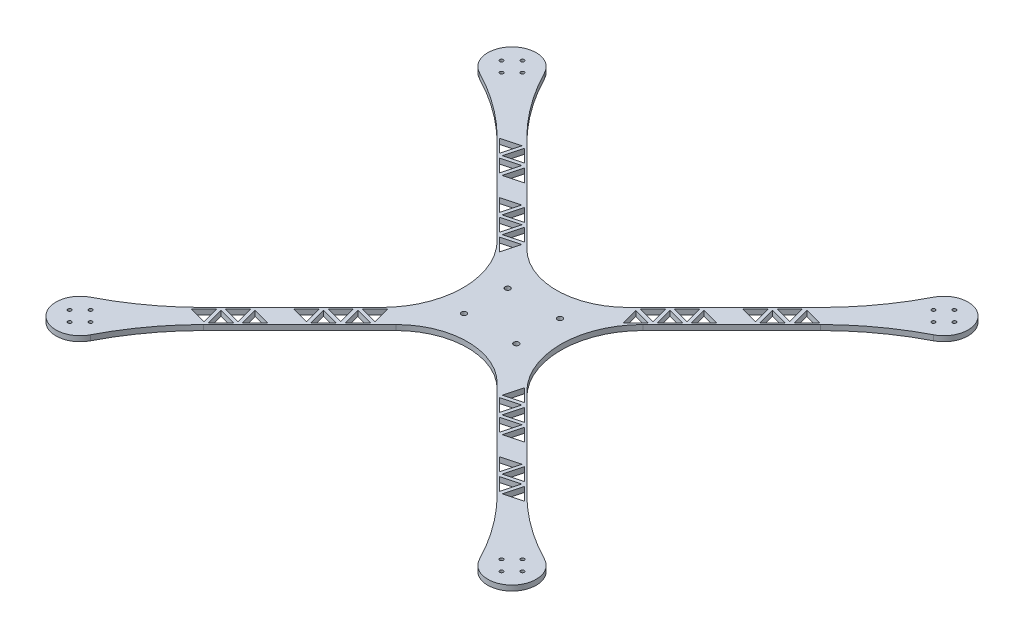
SolidWorks part; units mm, degrees
ref_plane "Front Plane" through (0, 0, 0) normal (0, 0, 1) x (1, 0, 0)
ref_plane "Top Plane" through (0, 0, 0) normal (0, 1, 0) x (1, 0, 0)
ref_plane "Right Plane" through (0, 0, 0) normal (1, 0, 0) x (0, 0, -1)
sketch "Sketch1" plane through (0, 0, 0) normal (0, 1, 0) x (1, 0, 0)
  line L0 (-18, 0) -> (18, 0) construction
  line L1 (-15, -15.5) -> (15, -15.5)
  line L2 (-18, -12.5) -> (-18, 12.5)
  line L3 (-15, 15.5) -> (15, 15.5)
  line L4 (18, -12.5) -> (18, 12.5)
  line L5 (-28, -12.5) -> (-28, 12.5)
  line L6 (-15, 25.5) -> (15, 25.5)
  line L7 (0, -15.5) -> (0, 15.5) construction
  line L8 (28, -12.5) -> (28, 12.5)
  line L9 (-15, -25.5) -> (15, -25.5)
  line L10 (123.7437, -123.7437) -> (-123.7437, 123.7437) construction
  line L11 (123.7437, 123.7437) -> (-123.7437, -123.7437) construction
  line L12 (127.9863, -119.501) -> (-119.501, 127.9863)
  line L13 (119.501, 127.9863) -> (-127.9863, -119.501)
  line L14 (119.501, -127.9863) -> (-127.9863, 119.501)
  line L15 (127.9863, 119.501) -> (-119.501, -127.9863)
  line L16 (-262.828, 0) -> (262.828, 0) construction
  circle A0 centre (15, 12.5) radius 1.5
  circle A1 centre (15, -12.5) radius 1.5
  circle A2 centre (-15, -12.5) radius 1.5
  circle A3 centre (-15, 12.5) radius 1.5
  arc A4 (15, 15.5) -> (18, 12.5) centre (15, 12.5) cw
  arc A5 (15, -15.5) -> (18, -12.5) centre (15, -12.5) ccw
  arc A6 (-15, -15.5) -> (-18, -12.5) centre (-15, -12.5) cw
  arc A7 (-18, 12.5) -> (-15, 15.5) centre (-15, 12.5) cw
  arc A12 (-28, 12.5) -> (-15, 25.5) centre (-15, 12.5) cw construction
  arc A13 (-15, -25.5) -> (-28, -12.5) centre (-15, -12.5) cw construction
  arc A14 (15, -25.5) -> (28, -12.5) centre (15, -12.5) ccw construction
  arc A15 (15, 25.5) -> (28, 12.5) centre (15, 12.5) cw construction
  circle A16 centre (123.7437, 123.7437) radius 13.85
  circle A17 centre (123.7437, -123.7437) radius 13.85
  circle A18 centre (-123.7437, -123.7437) radius 13.85
  circle A19 centre (-123.7437, 123.7437) radius 13.85
  arc A20 (111.4203, 130.0648) -> (84.1457, 92.631) centre (-21.4329, 198.2096) cw
  arc A21 (130.0648, 111.4203) -> (92.631, 84.1457) centre (198.2096, -21.4329) ccw
  arc A22 (41.799, 33.3137) -> (41.799, -33.3137) centre (75.1127, 0) ccw
  arc A23 (-41.799, 33.3137) -> (-41.799, -33.3137) centre (-75.1127, 0) cw
  arc A24 (111.4203, -130.0648) -> (84.1457, -92.631) centre (-21.4329, -198.2096) ccw
  arc A25 (130.0648, -111.4203) -> (92.631, -84.1457) centre (198.2096, 21.4329) cw
  arc A26 (-111.4203, 130.0648) -> (-84.1457, 92.631) centre (21.4329, 198.2096) ccw
  arc A27 (-130.0648, 111.4203) -> (-92.631, 84.1457) centre (-198.2096, -21.4329) cw
  arc A28 (-111.4203, -130.0648) -> (-84.1457, -92.631) centre (21.4329, -198.2096) cw
  arc A29 (-130.0648, -111.4203) -> (-92.631, -84.1457) centre (-198.2096, 21.4329) ccw
  arc A30 (-29.0459, 37.5312) -> (29.0459, 37.5312) centre (0, 66.5772) ccw
  arc A31 (-29.0459, -37.5312) -> (29.0459, -37.5312) centre (0, -66.5772) cw
  circle A32 centre (123.7437, 123.7437) radius 6 construction
  circle A36 centre (123.7437, 129.7437) radius 1
  circle A37 centre (129.7437, 123.7437) radius 1
  circle A38 centre (123.7437, 117.7437) radius 1
  circle A39 centre (117.7437, 123.7437) radius 1
  circle A40 centre (123.7437, -123.7437) radius 6 construction
  circle A41 centre (123.7437, -117.7437) radius 1
  circle A42 centre (129.7437, -123.7437) radius 1
  circle A43 centre (123.7437, -129.7437) radius 1
  circle A44 centre (117.7437, -123.7437) radius 1
  circle A45 centre (-123.7437, -123.7437) radius 6 construction
  circle A46 centre (-123.7437, -117.7437) radius 1
  circle A47 centre (-117.7437, -123.7437) radius 1
  circle A48 centre (-123.7437, -129.7437) radius 1
  circle A49 centre (-129.7437, -123.7437) radius 1
  circle A50 centre (-123.7437, 123.7437) radius 6 construction
  circle A51 centre (-123.7437, 129.7437) radius 1
  circle A52 centre (-117.7437, 123.7437) radius 1
  circle A53 centre (-123.7437, 117.7437) radius 1
  circle A54 centre (-129.7437, 123.7437) radius 1
  point P0 (0, 0)
  point P41 (0, 0)
  point P44 (0, 0)
  point P93 (-109.7065, 109.7065)
  point P99 (0, 0)
  point P108 (123.7437, 123.7437)
  point P118 (123.7437, -123.7437)
  point P128 (-123.7437, -123.7437)
  point P138 (-123.7437, 123.7437)
  dimension "D3" = 3
  dimension "D6" = 3
  dimension "D14" = 27.7
  dimension "D16" = 2
  dimension "D18" = 4
  dimension "D19" = 4
  dimension "D20" = 4
  dimension "D1" = 31
  dimension "D2" = 36
  dimension "D4" = 3
  dimension "D5" = 3
  dimension "D7" = 10
  dimension "D8" = 350
  dimension "D9" = 350
  dimension "D10" = 45
  dimension "D11" = 45
  dimension "D15" = 50
  dimension "D17" = 4
  dimension "D12" = 6
  dimension "D13" = 6
extrude "Boss-Extrude1" add sketch "Sketch1" along normal blind 3
sketch "Sketch3" plane through (0, 3, 0) normal (0, 1, 0) x (1, 0, 0)
  line L0 (-70.4196, 78.9048) -> (-83.8038, 75.3185)
  line L1 (-83.8038, 75.3185) -> (-74.0059, 65.5206)
  line L2 (-41.799, 33.3137) -> (-92.631, 84.1457) construction
  line L3 (-80.2201, 88.7053) -> (-93.6043, 85.119)
  line L8 (-93.6043, 85.119) -> (-83.8064, 75.3211)
  line L9 (-83.8064, 75.3211) -> (-80.2201, 88.7053)
  line L10 (-29.0459, 37.5312) -> (-84.1457, 92.631) construction
  line L11 (-123.7437, 123.7437) -> (0, 0) construction
  line L12 (-81.6343, 87.2911) -> (-91.6725, 84.6014)
  line L13 (-91.6725, 84.6014) -> (-84.324, 77.2529)
  line L14 (-84.324, 77.2529) -> (-81.6343, 87.2911)
  line L15 (-74.0059, 65.5206) -> (-70.4196, 78.9048)
  line L16 (-71.8338, 77.4906) -> (-81.872, 74.8009)
  line L17 (-81.872, 74.8009) -> (-74.5235, 67.4524)
  line L18 (-74.5235, 67.4524) -> (-71.8338, 77.4906)
  line L19 (-60.6191, 69.1043) -> (-74.0033, 65.518)
  line L20 (-74.0033, 65.518) -> (-64.2054, 55.7201)
  line L21 (-64.2054, 55.7201) -> (-60.6191, 69.1043)
  line L22 (-62.0333, 67.6901) -> (-72.0715, 65.0004)
  line L23 (-72.0715, 65.0004) -> (-64.723, 57.6519)
  line L24 (-64.723, 57.6519) -> (-62.0333, 67.6901)
  line L25 (-50.8186, 59.3038) -> (-64.2028, 55.7175)
  line L26 (-64.2028, 55.7175) -> (-54.4049, 45.9196)
  line L27 (-54.4049, 45.9196) -> (-50.8186, 59.3038)
  line L28 (-52.2328, 57.8896) -> (-62.271, 55.1999)
  line L29 (-62.271, 55.1999) -> (-54.9225, 47.8514)
  line L30 (-54.9225, 47.8514) -> (-52.2328, 57.8896)
  line L31 (-41.0181, 49.5033) -> (-54.4023, 45.917)
  line L32 (-54.4023, 45.917) -> (-44.6044, 36.1191)
  line L33 (-44.6044, 36.1191) -> (-41.0181, 49.5033)
  line L34 (-42.4323, 48.0891) -> (-52.4705, 45.3994)
  line L35 (-52.4705, 45.3994) -> (-45.122, 38.0509)
  line L36 (-45.122, 38.0509) -> (-42.4323, 48.0891)
  line L37 (-31.2176, 39.7028) -> (-44.6018, 36.1165)
  line L38 (-44.6018, 36.1165) -> (-34.8039, 26.3186)
  line L39 (-34.8039, 26.3186) -> (-31.2176, 39.7028)
  line L40 (-32.6318, 38.2886) -> (-42.67, 35.5989)
  line L41 (-42.67, 35.5989) -> (-35.3215, 28.2504)
  line L42 (-35.3215, 28.2504) -> (-32.6318, 38.2886)
  line L43 (-80.2201, 88.7053) -> (-31.2176, 39.7028)
  line L44 (-59.2048, 70.5186) -> (-74.2621, 66.484) construction
  line L45 (-79.7024, 86.7735) -> (-72.3514, 79.4225)
  line L46 (-33.1494, 40.2205) -> (-43.1911, 37.5298)
  line L47 (-73.0399, 65.2618) -> (-72.8914, 65.816)
  line L48 (-72.3514, 79.4225) -> (-82.3931, 76.7318)
  line L49 (-63.2394, 55.4613) -> (-63.0909, 56.0155)
  line L50 (-62.5509, 69.622) -> (-72.5926, 66.9313)
  line L51 (-52.9916, 47.3303) -> (-50.3009, 57.372)
  line L52 (-52.7504, 59.8215) -> (-62.7921, 57.1308)
  line L53 (-43.1911, 37.5298) -> (-40.5004, 47.5715)
  line L54 (-42.9499, 50.021) -> (-52.9916, 47.3303)
  line L55 (-73.0399, 65.2618) -> (-69.0053, 80.3191) construction
  line L56 (-69.0053, 80.3191) -> (-84.0626, 76.2845) construction
  line L57 (-69.9019, 76.973) -> (-62.5509, 69.622)
  line L58 (-79.7024, 86.7735) -> (-33.1494, 40.2205) construction
  line L59 (-82.3931, 76.7318) -> (-79.7024, 86.7735)
  line L60 (-82.8404, 75.0623) -> (-79.7024, 86.7735) construction
  line L61 (-63.2394, 55.4613) -> (-59.2048, 70.5186) construction
  line L62 (-49.4043, 60.7181) -> (-64.4616, 56.6835) construction
  line L63 (-53.4389, 45.6608) -> (-49.4043, 60.7181) construction
  line L64 (-39.6038, 50.9176) -> (-54.6611, 46.883) construction
  line L65 (-43.6384, 35.8603) -> (-39.6038, 50.9176) construction
  line L66 (-60.1014, 67.1725) -> (-52.7504, 59.8215)
  line L67 (-50.3009, 57.372) -> (-42.9499, 50.021)
  line L68 (-40.5004, 47.5715) -> (-33.1494, 40.2205)
  line L69 (-62.7921, 57.1308) -> (-60.1014, 67.1725)
  line L70 (-33.1494, 40.2205) -> (-44.8606, 37.0825) construction
  line L71 (-63.9074, 56.832) -> (-64.4616, 56.6835)
  line L72 (-72.5926, 66.9313) -> (-69.9019, 76.973)
  line L73 (-73.7079, 66.6325) -> (-74.2621, 66.484)
  line L74 (-58.2257, -49.7404) -> (-68.0236, -59.5383)
  line L75 (-68.0262, -59.5409) -> (-77.8241, -69.3388)
  line L76 (-97.4251, -88.9398) -> (-84.0408, -92.5261)
  line L77 (-57.1112, -50.0358) -> (-57.2597, -49.4816)
  line L78 (-35.0383, -43.5236) -> (-38.6247, -30.1394)
  line L79 (-95.4933, -88.4222) -> (-85.4551, -91.1119)
  line L80 (-63.9222, -70.9933) -> (-66.6129, -60.9516)
  line L81 (-66.0918, -59.0207) -> (-56.0536, -61.7104)
  line L82 (-75.6546, -81.3114) -> (-78.3443, -71.2732)
  line L83 (-88.1448, -81.0737) -> (-95.4933, -88.4222)
  line L84 (-48.9428, -41.8717) -> (-56.2913, -49.2202)
  line L85 (-56.2913, -49.2202) -> (-46.2531, -51.9099)
  line L86 (-76.4134, -70.7521) -> (-66.3717, -73.4428)
  line L87 (-46.7707, -53.8418) -> (-54.1217, -61.1928)
  line L88 (-58.2231, -49.7378) -> (-44.8388, -53.3241)
  line L89 (-64.4398, -72.9251) -> (-68.0262, -59.5409)
  line L90 (-77.8267, -69.3414) -> (-87.6246, -79.1393)
  line L91 (-56.8124, -51.1511) -> (-46.7707, -53.8418)
  line L92 (-46.4908, -39.4197) -> (-36.4526, -42.1094)
  line L93 (-84.0408, -92.5261) -> (-87.6272, -79.1419)
  line L94 (-58.4819, -50.7038) -> (-57.9277, -50.8523)
  line L95 (-68.0236, -59.5383) -> (-54.6393, -63.1246)
  line L96 (-44.3212, -51.3923) -> (-47.0119, -41.3506)
  line L97 (-66.3717, -73.4428) -> (-73.7227, -80.7938)
  line L98 (-39.1423, -32.0712) -> (-46.4908, -39.4197)
  line L99 (-65.8541, -71.5109) -> (-68.5438, -61.4727)
  line L100 (-85.6928, -78.6217) -> (-75.6546, -81.3114)
  line L101 (-86.2139, -80.5526) -> (-76.1722, -83.2433)
  line L102 (-36.4526, -42.1094) -> (-39.1423, -32.0712)
  line L103 (-58.7433, -51.6722) -> (-66.0918, -59.0207)
  line L104 (-87.6272, -79.1419) -> (-97.4251, -88.9398)
  line L105 (-66.9117, -59.8363) -> (-67.0602, -59.2821)
  line L106 (-38.6247, -30.1394) -> (-48.4226, -39.9373)
  line L107 (-85.4551, -91.1119) -> (-88.1448, -81.0737)
  line L108 (-35.0383, -43.5236) -> (-84.0408, -92.5261)
  line L109 (-46.2531, -51.9099) -> (-48.9428, -41.8717)
  line L110 (-83.5232, -90.5943) -> (-86.2139, -80.5526)
  line L111 (-47.0119, -41.3506) -> (-36.9702, -44.0413)
  line L112 (-56.0536, -61.7104) -> (-58.7433, -51.6722)
  line L113 (-54.1217, -61.1928) -> (-56.8124, -51.1511)
  line L114 (-66.6129, -60.9516) -> (-56.5712, -63.6423)
  line L115 (-54.6393, -63.1246) -> (-58.2257, -49.7404)
  line L116 (-78.3443, -71.2732) -> (-85.6928, -78.6217)
  line L117 (-76.1722, -83.2433) -> (-83.5232, -90.5943)
  line L118 (-68.5438, -61.4727) -> (-75.8923, -68.8212)
  line L119 (-74.2403, -82.7256) -> (-77.8267, -69.3414)
  line L120 (0, 0) -> (-123.7437, -123.7437) construction
  line L121 (-44.8388, -53.3241) -> (-48.4252, -39.9399)
  line L122 (-36.9702, -44.0413) -> (-44.3212, -51.3923)
  line L123 (-73.7227, -80.7938) -> (-76.4134, -70.7521)
  line L124 (-77.8241, -69.3388) -> (-64.4398, -72.9251)
  line L125 (-75.8923, -68.8212) -> (-65.8541, -71.5109)
  line L126 (-68.2824, -60.5043) -> (-67.7282, -60.6528)
  line L127 (-48.4252, -39.9399) -> (-58.2231, -49.7378)
  line L128 (-48.4226, -39.9373) -> (-35.0383, -43.5236)
  line L129 (-87.6246, -79.1393) -> (-74.2403, -82.7256)
  line L130 (-56.5712, -63.6423) -> (-63.9222, -70.9933)
  line L131 (0, -178.1578) -> (0, 178.1578) construction
  line L132 (0, 0) -> (123.7437, -123.7437) construction
  line L133 (123.7437, 123.7437) -> (0, 0) construction
  line L134 (56.5712, -63.6423) -> (63.9222, -70.9933)
  line L135 (87.6246, -79.1393) -> (74.2403, -82.7256)
  line L136 (48.4226, -39.9373) -> (35.0383, -43.5236)
  line L137 (48.4252, -39.9399) -> (58.2231, -49.7378)
  line L138 (68.2824, -60.5043) -> (67.7282, -60.6528)
  line L139 (75.8923, -68.8212) -> (65.8541, -71.5109)
  line L140 (77.8241, -69.3388) -> (64.4398, -72.9251)
  line L141 (73.7227, -80.7938) -> (76.4134, -70.7521)
  line L142 (36.9702, -44.0413) -> (44.3212, -51.3923)
  line L143 (44.8388, -53.3241) -> (48.4252, -39.9399)
  line L144 (74.2403, -82.7256) -> (77.8267, -69.3414)
  line L145 (68.5438, -61.4727) -> (75.8923, -68.8212)
  line L146 (76.1722, -83.2433) -> (83.5232, -90.5943)
  line L147 (78.3443, -71.2732) -> (85.6928, -78.6217)
  line L148 (54.6393, -63.1246) -> (58.2257, -49.7404)
  line L149 (66.6129, -60.9516) -> (56.5712, -63.6423)
  line L150 (54.1217, -61.1928) -> (56.8124, -51.1511)
  line L151 (56.0536, -61.7104) -> (58.7433, -51.6722)
  line L152 (47.0119, -41.3506) -> (36.9702, -44.0413)
  line L153 (83.5232, -90.5943) -> (86.2139, -80.5526)
  line L154 (46.2531, -51.9099) -> (48.9428, -41.8717)
  line L155 (35.0383, -43.5236) -> (84.0408, -92.5261)
  line L156 (85.4551, -91.1119) -> (88.1448, -81.0737)
  line L157 (38.6247, -30.1394) -> (48.4226, -39.9373)
  line L158 (66.9117, -59.8363) -> (67.0602, -59.2821)
  line L159 (87.6272, -79.1419) -> (97.4251, -88.9398)
  line L160 (58.7433, -51.6722) -> (66.0918, -59.0207)
  line L161 (36.4526, -42.1094) -> (39.1423, -32.0712)
  line L162 (86.2139, -80.5526) -> (76.1722, -83.2433)
  line L163 (85.6928, -78.6217) -> (75.6546, -81.3114)
  line L164 (65.8541, -71.5109) -> (68.5438, -61.4727)
  line L165 (39.1423, -32.0712) -> (46.4908, -39.4197)
  line L166 (66.3717, -73.4428) -> (73.7227, -80.7938)
  line L167 (44.3212, -51.3923) -> (47.0119, -41.3506)
  line L168 (68.0236, -59.5383) -> (54.6393, -63.1246)
  line L169 (58.4819, -50.7038) -> (57.9277, -50.8523)
  line L170 (84.0408, -92.5261) -> (87.6272, -79.1419)
  line L171 (46.4908, -39.4197) -> (36.4526, -42.1094)
  line L172 (56.8124, -51.1511) -> (46.7707, -53.8418)
  line L173 (77.8267, -69.3414) -> (87.6246, -79.1393)
  line L174 (64.4398, -72.9251) -> (68.0262, -59.5409)
  line L175 (58.2231, -49.7378) -> (44.8388, -53.3241)
  line L176 (46.7707, -53.8418) -> (54.1217, -61.1928)
  line L177 (76.4134, -70.7521) -> (66.3717, -73.4428)
  line L178 (56.2913, -49.2202) -> (46.2531, -51.9099)
  line L179 (48.9428, -41.8717) -> (56.2913, -49.2202)
  line L180 (88.1448, -81.0737) -> (95.4933, -88.4222)
  line L181 (75.6546, -81.3114) -> (78.3443, -71.2732)
  line L182 (66.0918, -59.0207) -> (56.0536, -61.7104)
  line L183 (63.9222, -70.9933) -> (66.6129, -60.9516)
  line L184 (95.4933, -88.4222) -> (85.4551, -91.1119)
  line L185 (35.0383, -43.5236) -> (38.6247, -30.1394)
  line L186 (57.1112, -50.0358) -> (57.2597, -49.4816)
  line L187 (97.4251, -88.9398) -> (84.0408, -92.5261)
  line L188 (68.0262, -59.5409) -> (77.8241, -69.3388)
  line L189 (58.2257, -49.7404) -> (68.0236, -59.5383)
  line L190 (73.7079, 66.6325) -> (74.2621, 66.484)
  line L191 (72.5926, 66.9313) -> (69.9019, 76.973)
  line L192 (63.9074, 56.832) -> (64.4616, 56.6835)
  line L193 (62.7921, 57.1308) -> (60.1014, 67.1725)
  line L194 (40.5004, 47.5715) -> (33.1494, 40.2205)
  line L195 (50.3009, 57.372) -> (42.9499, 50.021)
  line L196 (60.1014, 67.1725) -> (52.7504, 59.8215)
  line L197 (82.3931, 76.7318) -> (79.7024, 86.7735)
  line L198 (69.9019, 76.973) -> (62.5509, 69.622)
  line L199 (42.9499, 50.021) -> (52.9916, 47.3303)
  line L200 (43.1911, 37.5298) -> (40.5004, 47.5715)
  line L201 (52.7504, 59.8215) -> (62.7921, 57.1308)
  line L202 (52.9916, 47.3303) -> (50.3009, 57.372)
  line L203 (62.5509, 69.622) -> (72.5926, 66.9313)
  line L204 (63.2394, 55.4613) -> (63.0909, 56.0155)
  line L205 (72.3514, 79.4225) -> (82.3931, 76.7318)
  line L206 (73.0399, 65.2618) -> (72.8914, 65.816)
  line L207 (33.1494, 40.2205) -> (43.1911, 37.5298)
  line L208 (79.7024, 86.7735) -> (72.3514, 79.4225)
  line L209 (80.2201, 88.7053) -> (31.2176, 39.7028)
  line L210 (35.3215, 28.2504) -> (32.6318, 38.2886)
  line L211 (42.67, 35.5989) -> (35.3215, 28.2504)
  line L212 (32.6318, 38.2886) -> (42.67, 35.5989)
  line L213 (34.8039, 26.3186) -> (31.2176, 39.7028)
  line L214 (44.6018, 36.1165) -> (34.8039, 26.3186)
  line L215 (31.2176, 39.7028) -> (44.6018, 36.1165)
  line L216 (45.122, 38.0509) -> (42.4323, 48.0891)
  line L217 (52.4705, 45.3994) -> (45.122, 38.0509)
  line L218 (42.4323, 48.0891) -> (52.4705, 45.3994)
  line L219 (44.6044, 36.1191) -> (41.0181, 49.5033)
  line L220 (54.4023, 45.917) -> (44.6044, 36.1191)
  line L221 (41.0181, 49.5033) -> (54.4023, 45.917)
  line L222 (54.9225, 47.8514) -> (52.2328, 57.8896)
  line L223 (62.271, 55.1999) -> (54.9225, 47.8514)
  line L224 (52.2328, 57.8896) -> (62.271, 55.1999)
  line L225 (54.4049, 45.9196) -> (50.8186, 59.3038)
  line L226 (64.2028, 55.7175) -> (54.4049, 45.9196)
  line L227 (50.8186, 59.3038) -> (64.2028, 55.7175)
  line L228 (64.723, 57.6519) -> (62.0333, 67.6901)
  line L229 (72.0715, 65.0004) -> (64.723, 57.6519)
  line L230 (62.0333, 67.6901) -> (72.0715, 65.0004)
  line L231 (64.2054, 55.7201) -> (60.6191, 69.1043)
  line L232 (74.0033, 65.518) -> (64.2054, 55.7201)
  line L233 (60.6191, 69.1043) -> (74.0033, 65.518)
  line L234 (74.5235, 67.4524) -> (71.8338, 77.4906)
  line L235 (81.872, 74.8009) -> (74.5235, 67.4524)
  line L236 (71.8338, 77.4906) -> (81.872, 74.8009)
  line L237 (74.0059, 65.5206) -> (70.4196, 78.9048)
  line L238 (84.324, 77.2529) -> (81.6343, 87.2911)
  line L239 (91.6725, 84.6014) -> (84.324, 77.2529)
  line L240 (81.6343, 87.2911) -> (91.6725, 84.6014)
  line L241 (83.8064, 75.3211) -> (80.2201, 88.7053)
  line L242 (93.6043, 85.119) -> (83.8064, 75.3211)
  line L243 (80.2201, 88.7053) -> (93.6043, 85.119)
  line L244 (83.8038, 75.3185) -> (74.0059, 65.5206)
  line L245 (70.4196, 78.9048) -> (83.8038, 75.3185)
  circle A0 centre (-76.0764, 73.248) radius 4 construction
  circle A1 centre (-85.8769, 83.0485) radius 4 construction
  circle A2 centre (-66.2759, 63.4475) radius 4 construction
  circle A3 centre (-56.4754, 53.647) radius 4 construction
  circle A4 centre (-46.6749, 43.8465) radius 4 construction
  circle A5 centre (-36.8744, 34.046) radius 4 construction
  circle A6 centre (-70.0967, -67.2683) radius 4 construction
  circle A7 centre (-40.6952, -37.8668) radius 4 construction
  circle A8 centre (-60.2962, -57.4678) radius 4 construction
  circle A9 centre (-50.4957, -47.6673) radius 4 construction
  circle A10 centre (-79.8972, -77.0688) radius 4 construction
  circle A11 centre (-89.6977, -86.8693) radius 4 construction
  circle A12 centre (89.6977, -86.8693) radius 4 construction
  circle A13 centre (79.8972, -77.0688) radius 4 construction
  circle A14 centre (50.4957, -47.6673) radius 4 construction
  circle A15 centre (60.2962, -57.4678) radius 4 construction
  circle A16 centre (40.6952, -37.8668) radius 4 construction
  circle A17 centre (70.0967, -67.2683) radius 4 construction
  circle A18 centre (36.8744, 34.046) radius 4 construction
  circle A19 centre (46.6749, 43.8465) radius 4 construction
  circle A20 centre (56.4754, 53.647) radius 4 construction
  circle A21 centre (66.2759, 63.4475) radius 4 construction
  circle A22 centre (85.8769, 83.0485) radius 4 construction
  circle A23 centre (76.0764, 73.248) radius 4 construction
  point P164 (0, 0)
  dimension "D2" = 13.8564
  dimension "D1" = 1
  dimension "D4" = 1
  dimension "D3" = 6
extrude "Cut-Extrude1" cut sketch "Sketch3" against normal blind 10 contours L41 L42 L40 | L68 L53 L46 | L35 L36 L34 | L67 L51 L54 | L29 L30 L28 | L72 L50 L57 | L17 L18 L16 | L59 L48 L45 | L13 L14 L12 | L240 L238 L239 | L197 L208 L205 | L236 L234 L235 | L198 L203 L191 | L224 L222 L223 | L199 L202 L195 | L218 L216 L217 | L194 L207 L200 | L212 L210 L211 | L184 L180 L156 | L153 L162 L146 | L181 L163 L147 | L141 L177 L166 | L182 L160 L151 | L172 L176 L150 | L179 L154 L178 | L142 L167 L152 | L171 L165 L161 | L79 L107 L83 | L117 L101 L110 | L82 L116 L100 | L123 L97 L86 | L81 L112 L103 | L113 L87 L91 | L85 L109 L84 | L122 L111 L96 | L92 L102 L98
